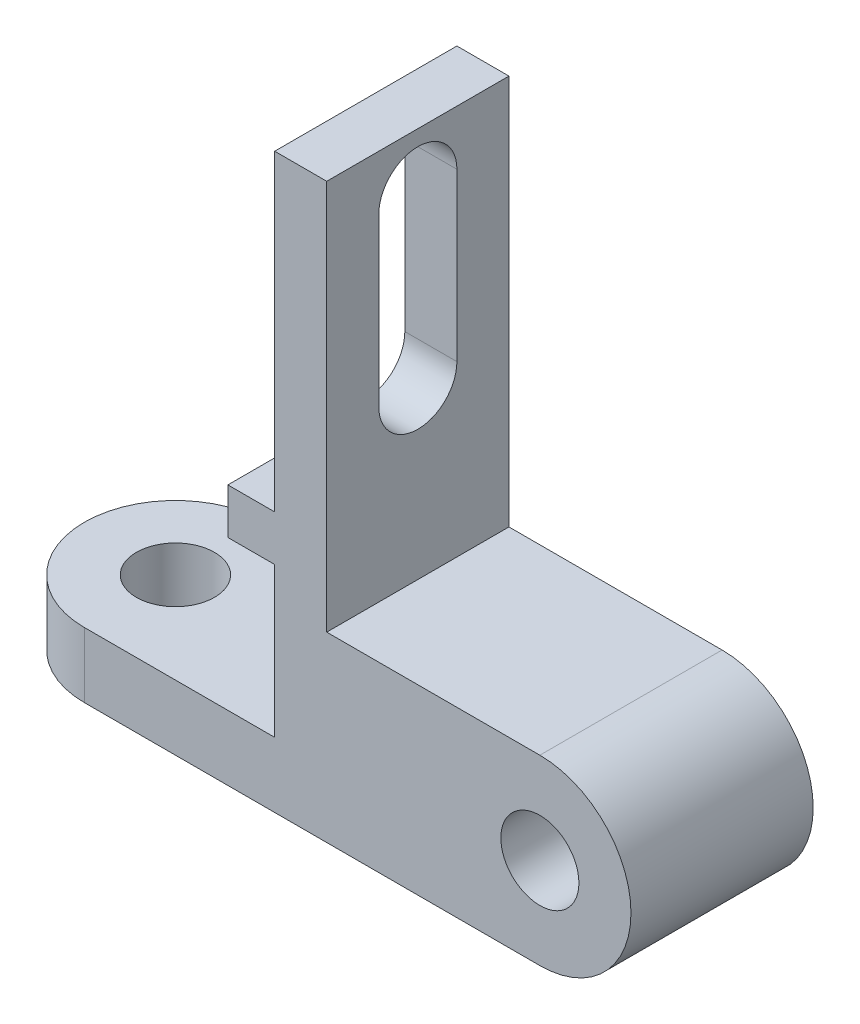
SolidWorks part; units mm, degrees
ref_plane "Front Plane" through (0, 0, 0) normal (0, 0, 1) x (1, 0, 0)
ref_plane "Top Plane" through (0, 0, 0) normal (0, 1, 0) x (1, 0, 0)
ref_plane "Right Plane" through (0, 0, 0) normal (1, 0, 0) x (0, 0, -1)
sketch "Sketch1" plane through (0, 0, 0) normal (0, 0, 1) x (1, 0, 0)
  line L0 (0, -14) -> (-70, -14)
  line L1 (-70, -14) -> (-70, -4)
  line L2 (-70, -4) -> (-40.7493, -4)
  line L3 (-40.7493, -4) -> (-40.7493, 19)
  line L4 (-40.7493, 19) -> (-47.9404, 19)
  line L5 (-47.9404, 19) -> (-47.9404, 26)
  line L6 (-47.9404, 26) -> (-40.7493, 26)
  line L7 (-40.7493, 26) -> (-40.7493, 74)
  line L8 (-40.7493, 74) -> (-32.7493, 74)
  line L9 (-32.7493, 74) -> (-32.7493, 14)
  line L10 (-32.7493, 14) -> (0, 14)
  arc A0 (0, -14) -> (0, 14) centre (0, 0) ccw
  circle A1 centre (0, 0) radius 6
  point P1 (-44.3448, 26)
  dimension "D1" = 28
  dimension "D2" = 12
  dimension "D3" = 70
  dimension "D4" = 8
  dimension "D5" = 48
  dimension "D6" = 7
  dimension "D7" = 23
  dimension "D8" = 10
extrude "Boss-Extrude1" add sketch "Sketch1" along normal mid plane 28
sketch "Sketch3" plane through (0, -4, 0) normal (0, 1, 0) x (1, 0, 0)
  line L0 (-70, -14) -> (-70, 14) construction
  line L1 (-70, -14) -> (-70, 14)
  arc A0 (-70, 14) -> (-70, -14) centre (-70, 0) ccw
extrude "Boss-Extrude3" add sketch "Sketch3" against normal blind 10
sketch "Sketch4" plane through (0, -4, 0) normal (0, 1, 0) x (1, 0, 0)
  circle A0 centre (-70, 0) radius 6
  dimension "D1" = 12
extrude "Cut-Extrude1" cut sketch "Sketch4" against normal blind 10
sketch "Sketch5" plane through (-32.7493, 0, 0) normal (1, 0, 0) x (0, 0, -1)
  line L0 (-14, 14) -> (14, 14) construction
  line L1 (-6, 65.5983) -> (-6, 40)
  line L2 (6, 65.5983) -> (6, 40)
  arc A0 (-6, 40) -> (6, 40) centre (0, 40) ccw
  arc A1 (6, 65.5983) -> (-6, 65.5983) centre (0, 65.5983) ccw
  dimension "D1" = 12
  dimension "D2" = 26
extrude "Cut-Extrude2" cut sketch "Sketch5" against normal blind 10
